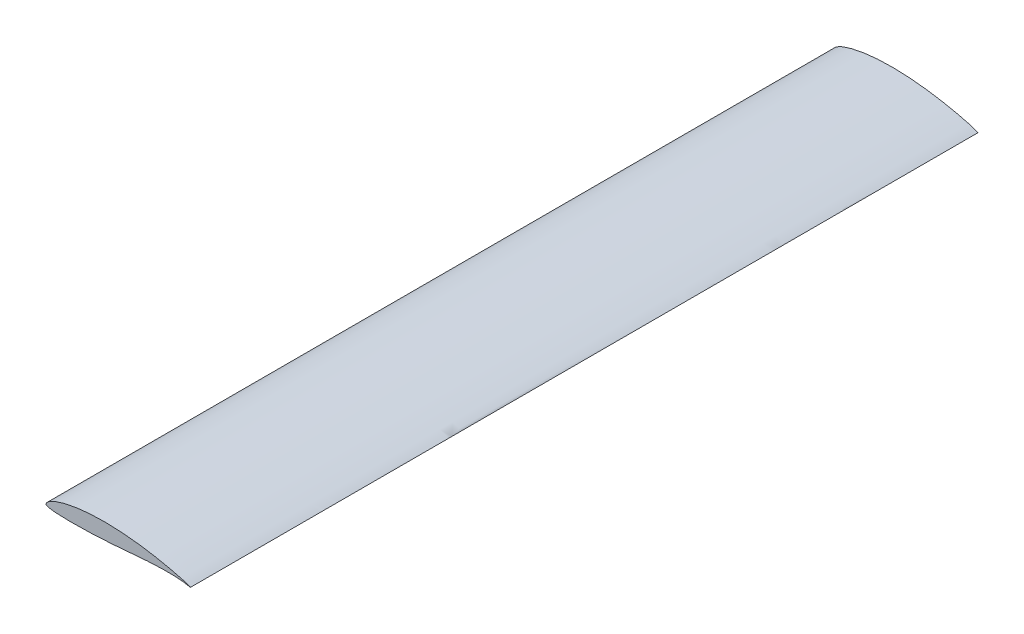
SolidWorks part; units mm, degrees
ref_plane "Front" through (0, 0, 0) normal (0, 0, 1) x (1, 0, 0)
ref_plane "Top" through (0, 0, 0) normal (0, 1, 0) x (1, 0, 0)
ref_plane "Right" through (0, 0, 0) normal (1, 0, 0) x (0, 0, -1)
curve "Curve8"
  spline degree 3 poles (0.9923, 0.002, 0) (1.0018, -0.0006, 0) (0.9935, 0.0025, 0) (0.9873, 0.0054, 0) (0.9729, 0.0112, 0) (0.9552, 0.0169, 0) (0.9323, 0.0235, 0) (0.9052, 0.0305, 0) (0.8739, 0.038, 0) (0.8389, 0.0459, 0) (0.8007, 0.0539, 0) (0.7597, 0.0618, 0) (0.7165, 0.0694, 0) (0.6715, 0.0764, 0) (0.6251, 0.0826, 0) (0.5777, 0.0878, 0) (0.5298, 0.0919, 0) (0.4817, 0.0947, 0) (0.434, 0.0963, 0) (0.387, 0.0965, 0) (0.3411, 0.0954, 0) (0.2968, 0.0929, 0) (0.2544, 0.089, 0) (0.2143, 0.084, 0) (0.1767, 0.0778, 0) (0.1421, 0.0707, 0) (0.1108, 0.0628, 0) (0.083, 0.0542, 0) (0.0589, 0.0452, 0) (0.0388, 0.036, 0) (0.0229, 0.0267, 0) (0.011, 0.0176, 0) (0.0036, 0.009, 0) (0.0001, 0.0029, 0) (-0.0001, -0.0017, 0) (0.003, -0.0068, 0) (0.0129, -0.0097, 0) (0.0271, -0.0136, 0) (0.0469, -0.0163, 0) (0.0716, -0.0186, 0) (0.1011, -0.0203, 0) (0.135, -0.0213, 0) (0.1731, -0.0216, 0) (0.2149, -0.0214, 0) (0.2598, -0.0205, 0) (0.3074, -0.019, 0) (0.3573, -0.0169, 0) (0.4088, -0.0142, 0) (0.4615, -0.0107, 0) (0.5152, -0.0064, 0) (0.5694, -0.0015, 0) (0.6237, 0.0033, 0) (0.6775, 0.0076, 0) (0.7299, 0.011, 0) (0.78, 0.0133, 0) (0.8269, 0.0143, 0) (0.8698, 0.0141, 0) (0.9076, 0.0128, 0) (0.9399, 0.0102, 0) (0.9646, 0.0072, 0) (0.9844, 0.0034, 0) (0.9923, 0.002, 0) (1.0018, -0.0006, 0) (0.9935, 0.0025, 0) knots -0.016249 -0.007187 -0.001789 0 0.001694 0.006395 0.013462 0.022754 0.034367 0.048191 0.064031 0.081681 0.100894 0.121432 0.143025 0.165434 0.188439 0.211855 0.235496 0.259144 0.282615 0.305702 0.328232 0.35003 0.370944 0.390817 0.409506 0.426857 0.442733 0.457018 0.469615 0.48045 0.489472 0.49673 0.502329 0.506256 0.506442 0.509182 0.513914 0.521178 0.530944 0.543145 0.55767 0.574384 0.59311 0.613638 0.635744 0.659184 0.683714 0.709076 0.735036 0.76143 0.788184 0.815057 0.841645 0.867514 0.892232 0.915364 0.936485 0.9552 0.971104 0.983751 0.992813 0.998211 1 1.001694 1.006395 1.013462 periodic
sketch "Sketch1" plane through (0, 0, 0) normal (0, 0, 1) x (1, 0, 0)
  line L0 (0, 0) -> (0, 66.0832) construction
  line L1 (220, 0) -> (0, 0) construction
  spline S1 degree 3 poles (218.3157, 0.4349) (220.3993, -0.1274) (218.5639, 0.5431) (217.2029, 1.1952) (214.0319, 2.457) (210.1515, 3.7257) (205.115, 5.1598) (199.1499, 6.7121) (192.2618, 8.3704) (184.5671, 10.095) (176.1575, 11.8481) (167.1441, 13.5891) (157.6314, 15.2613) (147.7241, 16.8116) (137.5145, 18.1799) (127.091, 19.3176) (116.5473, 20.2114) (105.9762, 20.8431) (95.4746, 21.1854) (85.1348, 21.2321) (75.048, 20.984) (65.2988, 20.4309) (55.9697, 19.5866) (47.1378, 18.4718) (38.8784, 17.1213) (31.267, 15.5525) (24.3698, 13.8158) (18.251, 11.9325) (12.962, 9.9537) (8.5428, 7.9201) (5.0331, 5.8837) (2.4128, 3.8632) (0.7958, 1.9768) (0.0193, 0.6443) (-0.0132, -0.3827) (0.6521, -1.4961) (2.8454, -2.1426) (5.9546, -2.9844) (10.3128, -3.5845) (15.7417, -4.1009) (22.2367, -4.4569) (29.7099, -4.676) (38.0856, -4.7585) (47.2678, -4.7016) (57.1538, -4.5115) (67.6355, -4.1888) (78.5994, -3.7204) (89.9344, -3.1183) (101.5395, -2.3573) (113.3403, -1.4148) (125.2654, -0.3266) (137.2227, 0.727) (149.0573, 1.6634) (160.5822, 2.4112) (171.6036, 2.9163) (181.921, 3.1569) (191.3516, 3.1115) (199.6685, 2.8138) (206.7825, 2.2512) (212.2109, 1.5826) (216.5627, 0.7577) (218.3157, 0.4349) (220.3993, -0.1274) (218.5639, 0.5431) knots -0.016249 -0.007187 -0.001789 0 0.001694 0.006395 0.013462 0.022754 0.034367 0.048191 0.064031 0.081681 0.100894 0.121432 0.143025 0.165434 0.188439 0.211855 0.235496 0.259144 0.282615 0.305702 0.328232 0.35003 0.370944 0.390817 0.409506 0.426857 0.442733 0.457018 0.469615 0.48045 0.489472 0.49673 0.502329 0.506256 0.506442 0.509182 0.513914 0.521178 0.530944 0.543145 0.55767 0.574384 0.59311 0.613638 0.635744 0.659184 0.683714 0.709076 0.735036 0.76143 0.788184 0.815057 0.841645 0.867514 0.892232 0.915364 0.936485 0.9552 0.971104 0.983751 0.992813 0.998211 1 1.001694 1.006395 1.013462 only from (220, 0) to (220, 0)
extrude "Boss-Extrude1" add sketch "Sketch1" along normal blind 1200
